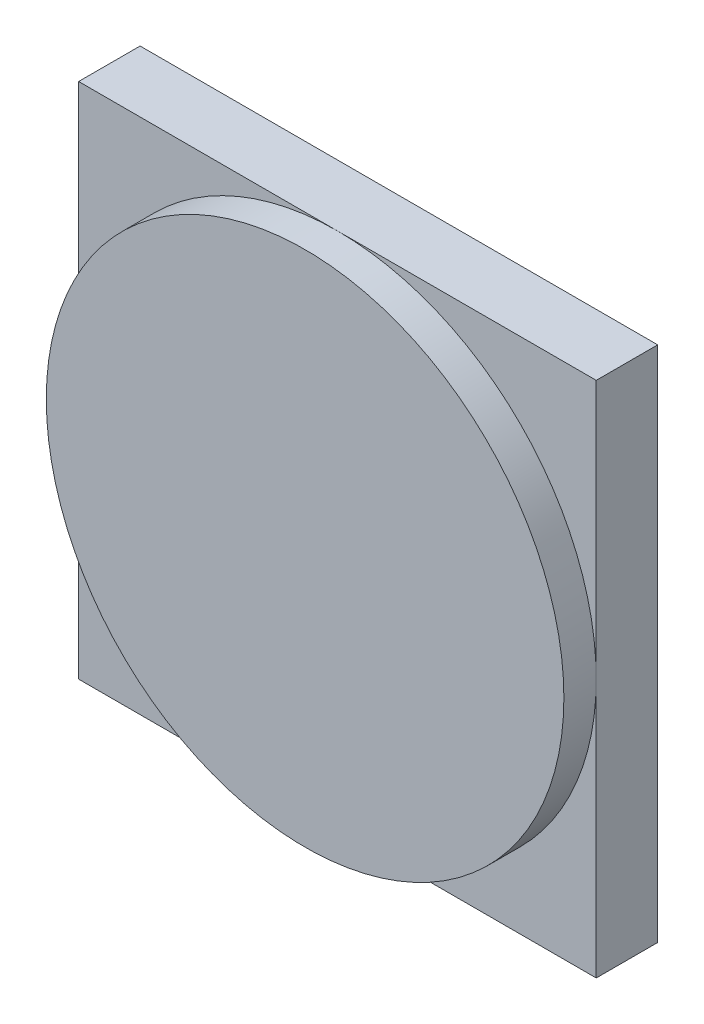
SolidWorks part; units mm, degrees
ref_plane "Front Plane" through (0, 0, 0) normal (1, 0, 0) x (0, 1, 0)
ref_plane "Top Plane" through (0, 0, 0) normal (0, 0, 1) x (0, 1, 0)
ref_plane "Right Plane" through (0, 0, 0) normal (0, 1, 0) x (-1, 0, 0)
sketch "Sketch1" plane through (0, 0, 0) normal (0, 0, 1) x (0, 1, 0)
  circle A0 centre (0, 0) radius 40
  dimension "D1" = 80
extrude "Boss-Extrude1" add sketch "Sketch1" along normal blind 5
sketch "Sketch2" plane through (0, 0, 0) normal (0, 0, -1) x (1, 0, 0)
  line L1 (-40, 40) -> (40, 40)
  line L2 (-40, 40) -> (-40, -40)
  line L3 (-40, -40) -> (40, -40)
  line L4 (40, 40) -> (40, -40)
  circle A0 centre (0, 0) radius 40 construction
  dimension "D1" = 80
extrude "Boss-Extrude2" add sketch "Sketch2" along normal blind 9.5
